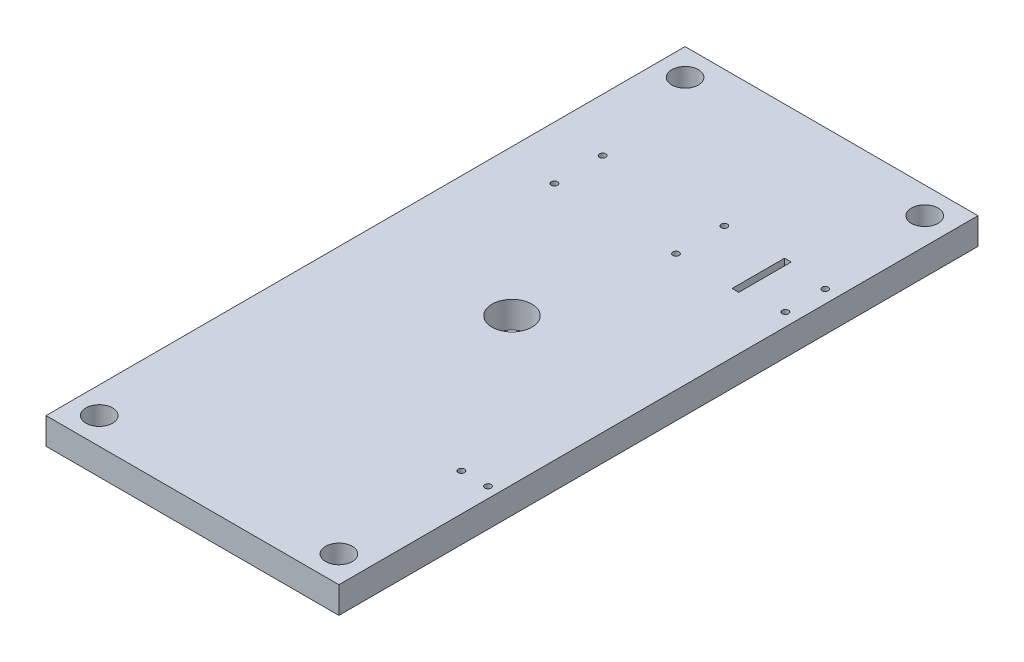
SolidWorks part; units mm, degrees
ref_plane "Front Plane" through (0, 0, 0) normal (0, 0, 1) x (1, 0, 0)
ref_plane "Top Plane" through (0, 0, 0) normal (0, 1, 0) x (1, 0, 0)
ref_plane "Right Plane" through (0, 0, 0) normal (1, 0, 0) x (0, 0, -1)
sketch "Sketch1" plane through (0, 0, 0) normal (0, 1, 0) x (1, 0, 0)
  line L1 (0, 0) -> (139.7, 0)
  line L2 (0, 0) -> (0, 304.8)
  line L3 (0, 304.8) -> (139.7, 304.8)
  line L4 (139.7, 0) -> (139.7, 304.8)
  dimension "D1" = 304.8
  dimension "D2" = 139.7
extrude "Boss-Extrude1" add sketch "Sketch1" along normal blind 12.7
sketch "Sketch5" plane through (0, 12.7, 0) normal (0, 1, 0) x (1, 0, 0)
  line L0 (0, 0) -> (139.7, 0) construction
  line L1 (69.85, 304.8) -> (69.85, 0) construction
  line L2 (139.7, 304.8) -> (0, 304.8) construction
  line L3 (0, 152.4) -> (69.85, 152.4) construction
  line L4 (0, 304.8) -> (0, 0) construction
  circle A16 centre (12.7, 12.7) radius 6.35
  circle A20 centre (127, 12.7) radius 6.35
  circle A21 centre (127, 292.1) radius 6.35
  circle A22 centre (12.7, 292.1) radius 6.35
  point P2 (0, 0)
  point P3 (0, 0)
  dimension "D12" = 12.7
  dimension "D13" = 12.7
  dimension "D14" = 12.7
extrude "Cut-Extrude2" cut sketch "Sketch5" against normal through all
hole_wizard "3/4 (0.7500) Dowel Hole1" positions "3DSketch1" profile "Sketch6" hole size "3/4" standard "ANSI Inch"
sketch3d "3DSketch1"
  line L2 (139.7, 12.7, 0) -> (139.7, 12.7, -304.8) construction
  line L4 (139.7, 12.7, -304.8) -> (0, 12.7, -304.8) construction
  point P0 (69.85, 12.7, -152.4)
  point P8 (0, 0, 0)
  point P11 (139.7, 12.7, -152.4)
  point P12 (0, 0, 0)
  point P16 (0, 0, 0)
  point P17 (64.7641, 12.7, -152.194)
  point P20 (69.85, 12.7, -304.8)
  point P21 (69.85, 12.7, -152.4)
sketch "Sketch6" plane through (69.85, 12.7, -152.4) normal (1, 0, 0) x (0, 0, 1)
  line L0 (0, 0) -> (0, 31.1232)
  line L1 (0, 31.1232) -> (9.525, 25.4)
  line L2 (9.525, 25.4) -> (9.525, 0)
  line L5 (9.525, 0) -> (0, 0)
  line L10 (0, 31.1232) -> (-9.525, 25.4) construction
  line L11 (0, -6.35) -> (0, 107.95) construction
  dimension "Hole Dia." = 19.05
  dimension "Hole Depth" = 25.4
  dimension "Drill Angle" = 118
sketch "Sketch10" plane through (0, 12.7, 0) normal (0, 1, 0) x (1, 0, 0)
  line L0 (0, 304.8) -> (0, 0) construction
  line L1 (25.4, 217.1) -> (83.4, 217.1) construction
  line L2 (25.4, 217.1) -> (25.4, 240.1) construction
  line L3 (25.4, 240.1) -> (83.4, 240.1) construction
  line L4 (83.4, 217.1) -> (83.4, 240.1) construction
  line L5 (0, 152.4) -> (0, 304.8) construction
  circle A0 centre (25.4, 217.1) radius 1.5
  circle A1 centre (25.4, 240.1) radius 1.5
  circle A2 centre (83.4, 240.1) radius 1.5
  circle A3 centre (83.4, 217.1) radius 1.5
  point P6 (25.4, 228.6)
  point P14 (0, 228.6)
  dimension "D4" = 3
  dimension "D5" = 3
  dimension "D6" = 3
  dimension "D7" = 3
  dimension "D1" = 58
  dimension "D2" = 23
  dimension "D3" = 25.4
extrude "Cut-Extrude3" cut sketch "Sketch10" against normal through all
sketch "Sketch11" plane through (0, 12.7, 0) normal (0, 1, 0) x (1, 0, 0)
  line L0 (139.7, 152.4) -> (139.7, 0) construction
  line L1 (139.7, 0) -> (139.7, 304.8) construction
  circle A0 centre (134.62, 76.2) radius 1.5
  circle A1 centre (121.92, 76.2) radius 1.5
  point P9 (139.7, 76.2)
  point P10 (0, 0)
  point P11 (96.3968, 51.5222)
  point P12 (0, 0)
  dimension "D3" = 3
  dimension "D4" = 3
  dimension "D1" = 5.08
  dimension "D2" = 12.7
extrude "Cut-Extrude4" cut sketch "Sketch11" against normal through all
sketch "Sketch12" plane through (0, 12.7, 0) normal (0, 1, 0) x (1, 0, 0)
  line L0 (139.7, 0) -> (139.7, 304.8) construction
  line L1 (139.7, 152.4) -> (139.7, 304.8) construction
  line L2 (133.52, 219.1) -> (133.52, 238.1) construction
  line L8 (111.125, 216.1) -> (114.3, 216.1)
  line L9 (111.125, 216.1) -> (111.125, 241.1)
  line L10 (111.125, 241.1) -> (114.3, 241.1)
  line L11 (114.3, 216.1) -> (114.3, 241.1)
  circle A0 centre (133.52, 219.1) radius 1.5
  circle A1 centre (133.52, 238.1) radius 1.5
  point P6 (133.52, 228.6)
  point P10 (139.7, 228.6)
  point P15 (114.3, 228.6)
  dimension "D3" = 3
  dimension "D4" = 3
  dimension "D1" = 6.18
  dimension "D2" = 19
  dimension "D5" = 25
  dimension "D6" = 3.175
  dimension "D7" = 25.4
extrude "Cut-Extrude6" cut sketch "Sketch12" against normal through all
